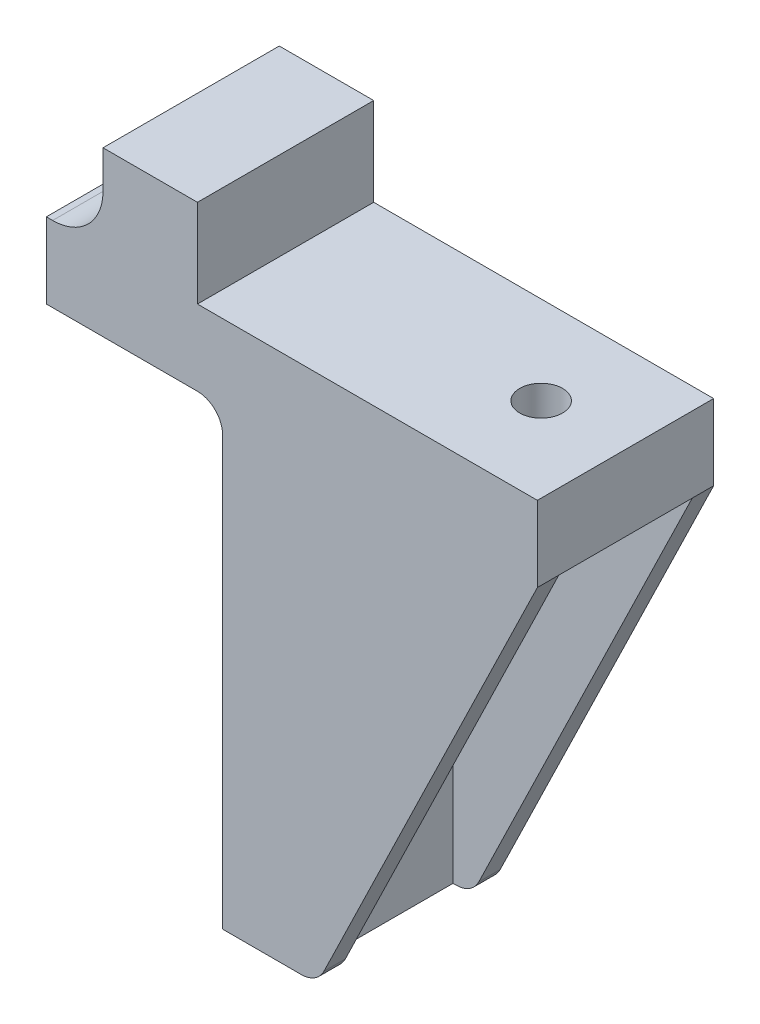
SolidWorks part; units mm, degrees
ref_plane "Front Plane" through (0, 0, 0) normal (0, 0, 1) x (1, 0, 0)
ref_plane "Top Plane" through (0, 0, 0) normal (0, 1, 0) x (1, 0, 0)
ref_plane "Right Plane" through (0, 0, 0) normal (1, 0, 0) x (0, 0, -1)
sketch "Sketch1" plane through (0, 0, 0) normal (0, 0, 1) x (1, 0, 0)
  line L1 (0, 0) -> (25, 0)
  line L2 (0, 0) -> (0, -5.5472)
  line L3 (6, -6) -> (25, -6)
  line L4 (25, 0) -> (25, -6)
  line L6 (0, -5.5472) -> (0, -42)
  line L7 (0, -42) -> (6, -42)
  line L8 (6, -6) -> (6, -42)
  point P8 (3, -42)
  dimension "D1" = 25
  dimension "D2" = 42
  dimension "D3" = 6
  dimension "D4" = 6
extrude "Boss-Extrude1" add sketch "Sketch1" along normal blind 14
sketch "Sketch2" plane through (6, 0, 0) normal (1, 0, 0) x (0, 0, -1)
  line L0 (-7, -6) -> (-7, -42) construction
  line L1 (-14, -6) -> (0, -6) construction
  line L2 (-14, -42) -> (0, -42) construction
  line L3 (-14, 0) -> (0, 0) construction
  circle A0 centre (-7, -17.78) radius 1.7
  circle A1 centre (-7, -34.058) radius 1.7
  dimension "D1" = 3.4
  dimension "D3" = 3.4
  dimension "D2" = 17.78
  dimension "D4" = 16.278
extrude "Cut-Extrude1" cut sketch "Sketch2" against normal blind 10
sketch "Sketch3" plane through (0, -6, 0) normal (0, -1, 0) x (1, 0, 0)
  line L0 (25, 7) -> (6, 7) construction
  line L1 (25, 14) -> (25, 0) construction
  line L2 (6, 14) -> (6, 0) construction
  circle A0 centre (18.3, 7) radius 1.7
  dimension "D1" = 3.4
  dimension "D2" = 6.7
extrude "Cut-Extrude2" cut sketch "Sketch3" against normal blind 10
sketch "Sketch14" plane through (0, 0, 0) normal (0, 0, -1) x (-1, 0, 0)
  line L1 (0, 0) -> (14, 0)
  line L2 (0, 0) -> (0, -6)
  line L3 (0, -6) -> (14, -6)
  line L4 (14, 0) -> (14, -6)
  dimension "D1" = 6
  dimension "D2" = 14
extrude "Boss-Extrude3" add sketch "Sketch14" against normal blind 14
fillet "Fillet8" radius 2 1 edges at (0, -6, 7)
sketch "Sketch17" plane through (0, -42, 0) normal (0, -1, 0) x (1, 0, 0)
  line L0 (6, 12.3) -> (7.5, 12.3)
  line L1 (6, 14) -> (7.5, 14)
  line L2 (6, 14) -> (6, 12.3)
  line L3 (6, 12.3) -> (7.5, 12.3)
  line L4 (7.5, 14) -> (7.5, 12.3)
  line L5 (6, 0) -> (7.5, 0)
  line L6 (6, 0) -> (6, 1.7)
  line L7 (6, 1.7) -> (7.5, 1.7)
  line L8 (7.5, 0) -> (7.5, 1.7)
  line L9 (6, 1.7) -> (7.5, 1.7)
  line L11 (6, 1.7) -> (6, 0)
  line L12 (6, 0) -> (25, 0)
  line L13 (25, 0) -> (25, 14)
  line L14 (25, 14) -> (6, 14)
  line L15 (6, 14) -> (6, 0)
  line L16 (6, 0) -> (7.5, 0)
  line L18 (7.5, 14) -> (6, 14)
  line L19 (6, 14) -> (6, 12.3)
  dimension "D1" = 1.5
  dimension "D2" = 1.5
  dimension "D3" = 1.7
  dimension "D4" = 1.7
  dimension "D5" = 0
sketch "Sketch18" plane through (0, -6, 0) normal (0, -1, 0) x (1, 0, 0)
  line L0 (6, 0) -> (25, 0) construction
  line L1 (6, 14) -> (6, 0) construction
  line L2 (6, 14) -> (25, 14) construction
  line L3 (25, 14) -> (25, 0) construction
  line L4 (6, 0) -> (25, 0)
  line L5 (6, 14) -> (6, 12.3)
  line L6 (6, 14) -> (25, 14)
  line L7 (25, 14) -> (25, 12.3)
  line L8 (6, 12.3) -> (25, 12.3)
  line L9 (6, 1.7) -> (25, 1.7)
  line L10 (25, 1.7) -> (25, 0)
  line L11 (6, 1.7) -> (6, 0)
loft "Loft2" add section "Sketch17" section "Sketch18"
sketch "Sketch19" plane through (0, -42, 0) normal (0, -1, 0) x (1, 0, 0)
  line L1 (6, 0) -> (7.5, 0)
  line L2 (6, 0) -> (6, 1.7)
  line L3 (6, 1.7) -> (7.5, 1.7)
  line L4 (7.5, 0) -> (7.5, 1.7)
  dimension "D1" = 1.5
  dimension "D2" = 1.7
sketch "Sketch20" plane through (0, -6, 0) normal (0, -1, 0) x (1, 0, 0)
  line L0 (25, 12.3) -> (25, 0) construction
  line L1 (6, 0) -> (25, 0)
  line L2 (6, 0) -> (6, 1.7)
  line L3 (6, 1.7) -> (25, 1.7)
  line L4 (25, 0) -> (25, 1.7)
  dimension "D1" = 1.7
loft "Loft3" add profiles "Sketch20", "Sketch19"
fillet "Fillet9" radius 8 1 edges
sketch "Sketch21" plane through (0, 0, 0) normal (0, 0, -1) x (-1, 0, 0)
  line L0 (-25, 0) -> (14, 0) construction
  line L1 (9.5, 0) -> (2, 0)
  line L2 (9.5, 0) -> (9.5, 7)
  line L3 (9.5, 7) -> (2, 7)
  line L4 (2, 0) -> (2, 7)
  line L5 (0, -8) -> (0, -42) construction
  point P8 (9.5, 0)
  dimension "D1" = 7
  dimension "D2" = 7.5
  dimension "D3" = 2
extrude "Boss-Extrude4" add sketch "Sketch21" against normal blind 14
fillet "Fillet10" radius 4 1 edges at (-9.5, 0, 7)
fillet "Fillet11" radius 2 1 edges
fillet "Fillet12" radius 2 1 edges
